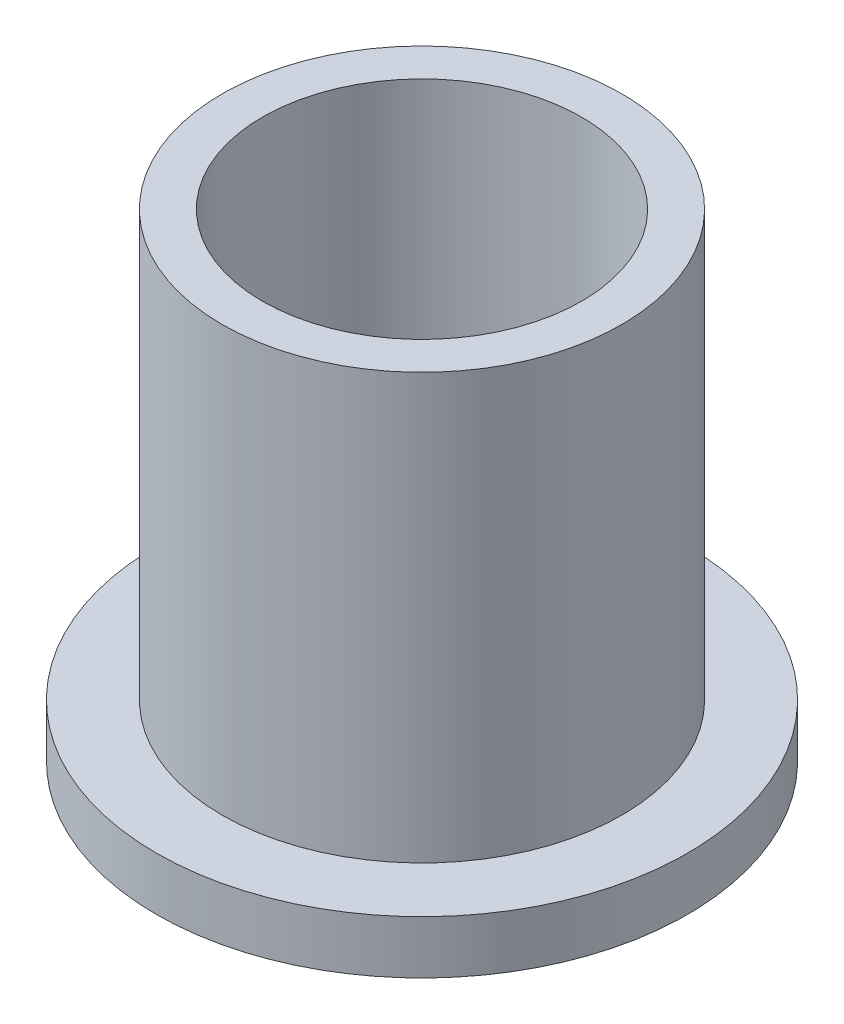
SolidWorks part; units mm, degrees
ref_plane "Front" through (0, 0, 0) normal (0, 0, 1) x (1, 0, 0)
ref_plane "Top" through (0, 0, 0) normal (0, 1, 0) x (1, 0, 0)
ref_plane "Right" through (0, 0, 0) normal (1, 0, 0) x (0, 0, -1)
sketch "Sketch1" plane through (0, 0, 0) normal (0, 1, 0) x (1, 0, 0)
  circle A0 centre (0, 0) radius 9.5377
  circle A1 centre (0, 0) radius 11.9444
  circle A2 centre (0, 0) radius 15.875
  dimension "ID" = 19.0754
  dimension "OD" = 23.8887
  dimension "FlangeOD" = 31.75
sketch "Sketch2" plane through (0, 0, 0) normal (0, 1, 0) x (1, 0, 0)
  circle A0 centre (0, 0) radius 9.5377 construction
  circle A1 centre (0, 0) radius 11.9444 construction
  circle A2 centre (0, 0) radius 9.5377
  circle A3 centre (0, 0) radius 11.9444
extrude "Boss-Extrude1" add sketch "Sketch2" along normal blind 28.575
sketch "Sketch3" plane through (0, 0, 0) normal (0, 1, 0) x (1, 0, 0)
  circle A0 centre (0, 0) radius 15.875 construction
  circle A1 centre (0, 0) radius 11.9444 construction
  circle A2 centre (0, 0) radius 15.875
  circle A3 centre (0, 0) radius 11.9444
extrude "Boss-Extrude2" add sketch "Sketch3" along normal blind 3.175
